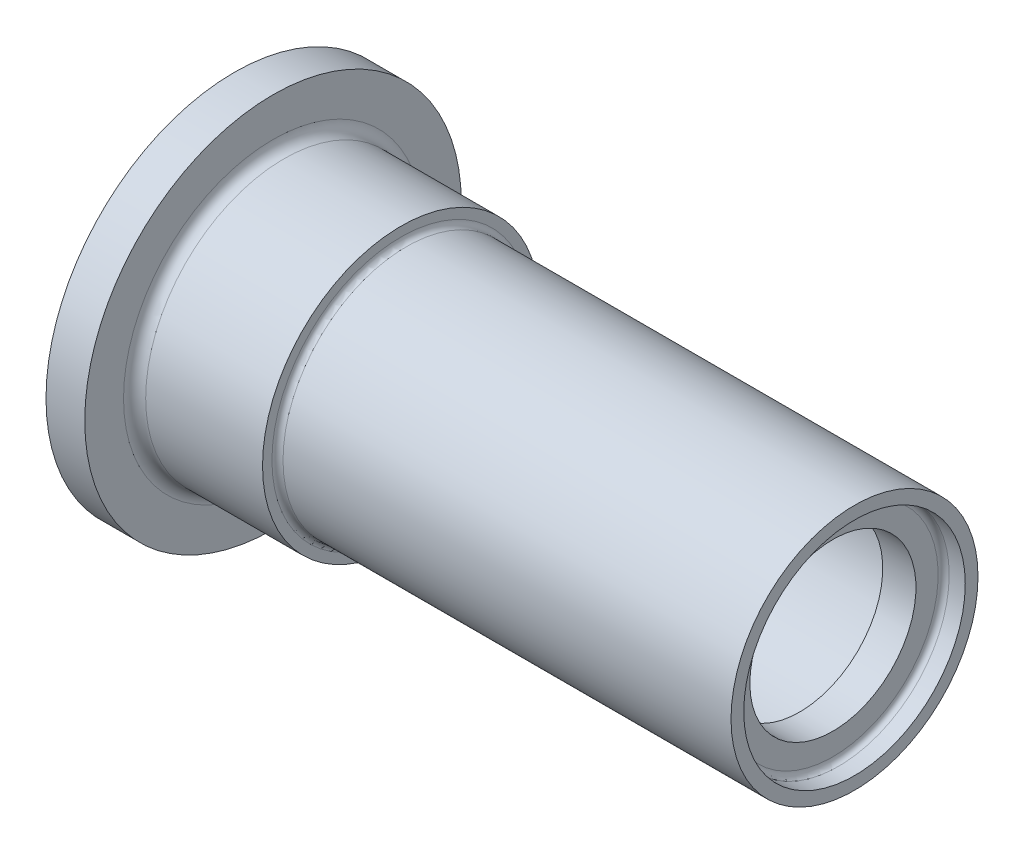
SolidWorks part; units mm, degrees
other "2D Pressure"
material "Polyetheretherketone (PEEK)"
ref_plane "Front Plane" through (0, 0, 0) normal (0, 0, 1) x (1, 0, 0)
ref_plane "Top Plane" through (0, 0, 0) normal (0, 1, 0) x (1, 0, 0)
ref_plane "Right Plane" through (0, 0, 0) normal (1, 0, 0) x (0, 0, -1)
ref_axis "Axis1" through (-88.99, 0, 0) along (1, 0, 0)
sketch "Sketch1" plane through (0, 0, 0) normal (0, 0, 1) x (1, 0, 0)
  line L0 (0, 12.5) -> (0, 11.65)
  line L1 (0.5, 11.15) -> (40.95, 11.15)
  line L3 (34.5, 10.15) -> (-13.55, 10.15)
  line L4 (-15.05, 15) -> (-15.05, 17)
  line L5 (-15.05, 17) -> (-11.55, 17)
  line L6 (-11.55, 17) -> (-11.55, 13.5)
  line L7 (-10.55, 12.5) -> (0, 12.5)
  line L8 (-88.99, 0) -> (88.99, 0) construction
  line L9 (-15.05, 15) -> (-14.05, 15)
  line L10 (-13.55, 14.5) -> (-13.55, 10.15)
  line L11 (36, 8.65) -> (36, 7.5)
  line L12 (36, 7.5) -> (39, 7.5)
  line L13 (39, 7.5) -> (39, 9.5)
  line L14 (39.5, 10) -> (40.95, 10)
  line L15 (40.95, 10) -> (40.95, 11.15)
  arc A0 (-14.05, 15) -> (-13.55, 14.5) centre (-14.05, 14.5) cw
  arc A1 (39, 9.5) -> (39.5, 10) centre (39.5, 9.5) cw
  arc A2 (36, 8.65) -> (34.5, 10.15) centre (34.5, 8.65) ccw
  arc A3 (0, 11.65) -> (0.5, 11.15) centre (0.5, 11.65) ccw
  arc A4 (-11.55, 13.5) -> (-10.55, 12.5) centre (-10.55, 13.5) ccw
  point P23 (36, 10.15)
  dimension "D9" = 0.5
  dimension "D14" = 0.5
  dimension "D16" = 1.5
  dimension "D17" = 0.5
  dimension "D18" = 1
  dimension "D1" = 22.3
  dimension "D2" = 1
  dimension "D3" = 25
  dimension "D4" = 3.5
  dimension "D5" = 30
  dimension "D6" = 34
  dimension "D7" = 36
  dimension "D8" = 1.5
  dimension "D10" = 56
  dimension "D11" = 15
  dimension "D12" = 20
  dimension "D13" = 1.95
  dimension "D15" = 3
revolve "Revolve1" add sketch "Sketch1" angle 360 about axis through (-88.99, 0, 0) along (1, 0, 0)
